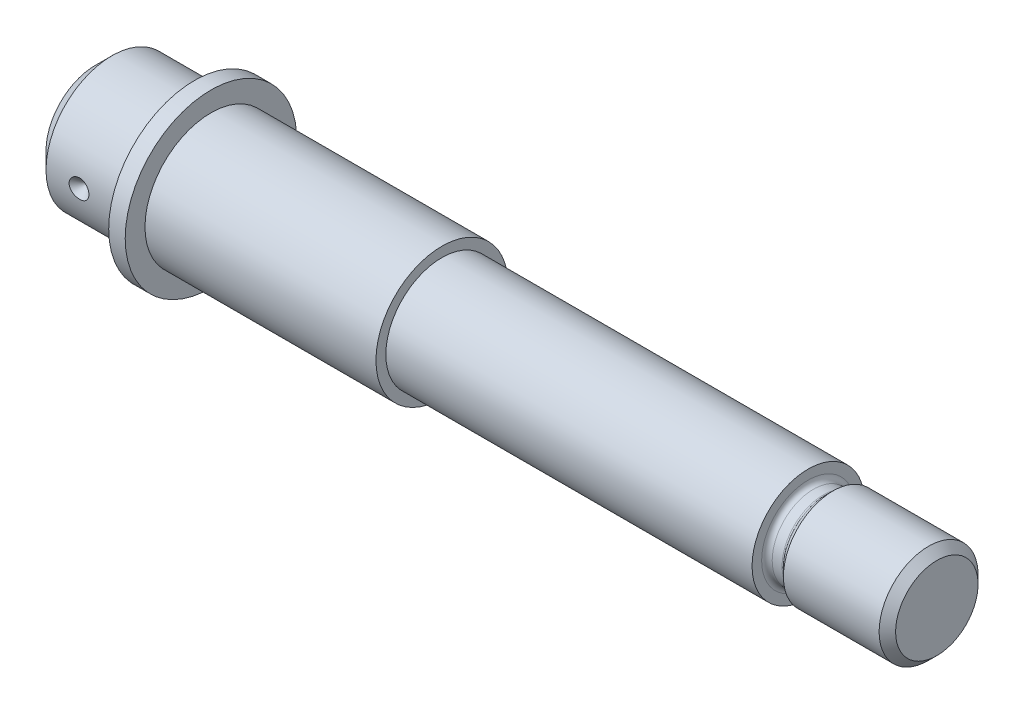
SolidWorks part; units mm, degrees
ref_plane "Front Plane" through (0, 0, 0) normal (0, 0, 1) x (1, 0, 0)
ref_plane "Top Plane" through (0, 0, 0) normal (0, 1, 0) x (1, 0, 0)
ref_plane "Right Plane" through (0, 0, 0) normal (1, 0, 0) x (0, 0, -1)
sketch "Sketch1" plane through (0, 0, 0) normal (0, 1, 0) x (1, 0, 0)
  line L0 (-87.7769, 0) -> (0, 0) construction
  line L1 (0, 0) -> (0, -15)
  line L2 (5, -20) -> (30, -20)
  line L3 (30, -20) -> (30, -26)
  line L4 (30, -26) -> (35, -26)
  line L5 (35, -26) -> (35, -20)
  line L6 (35, -20) -> (105, -20)
  line L7 (105, -20) -> (105, -17)
  line L8 (105, -17) -> (216, -17)
  line L9 (216, -17) -> (216, -15)
  line L10 (223.5, -15) -> (252.5, -15)
  line L11 (255, -12.5) -> (255, 0)
  line L12 (0, -15) -> (5, -20)
  line L13 (252.5, -15) -> (255, -12.5)
  line L14 (0, 0) -> (255, 0)
  line L15 (216, -15) -> (216, -14.1)
  line L16 (218.4967, -12.5) -> (217.6, -12.5) construction
  line L17 (30, -20) -> (35, -20) construction
  line L18 (216, -12.5) -> (216, -15) construction
  line L19 (217.6, -12.5) -> (220.5858, -12.5)
  line L20 (221.2929, -12.7929) -> (223.5, -15)
  line L21 (221, -12.5) -> (223.5, -12.5) construction
  line L22 (223.5, -12.5) -> (223.5, -15) construction
  arc A0 (216, -14.1) -> (217.6, -12.5) centre (217.6, -14.1) cw
  arc A2 (220.5858, -12.5) -> (221.2929, -12.7929) centre (220.5858, -13.5) cw
  point P4 (0, -20)
  point P15 (255, -15)
  point P24 (35, -23)
  point P26 (216, -12.5)
  point P34 (105, -18.5)
  dimension "D15" = 1.6
  dimension "D18" = 1
  dimension "D1" = 5
  dimension "D2" = 45
  dimension "D3" = 20
  dimension "D4" = 30
  dimension "D5" = 5
  dimension "D6" = 6
  dimension "D7" = 255
  dimension "D8" = 150
  dimension "D9" = 17
  dimension "D10" = 39
  dimension "D11" = 2.5
  dimension "D12" = 45
  dimension "D13" = 15
  dimension "D14" = 4.5
  dimension "D16" = 45
  dimension "D17" = 5
  dimension "D19" = 70
revolve "Revolve1" add sketch "Sketch1" angle 360 about L0
cosmetic thread "Cosmetic Thread1" parameters "D2"=26.2318
ref_plane "Plane1" through (0, 0, 20) normal (0, 0, 1) x (1, 0, 0)
sketch "Sketch4" plane through (0, 0, 20) normal (0, 0, 1) x (1, 0, 0)
  line L0 (5, 0) -> (30, 0) construction
  line L1 (5, 20) -> (5, -20) construction
  line L2 (30, 26) -> (30, -26) construction
  point P6 (15, 0)
  dimension "D1" = 10
ref_plane "Plane2" through (15, 0, 0) normal (-1, 0, 0) x (0, 0, 1)
sketch "Sketch5" plane through (15, 0, 0) normal (-1, 0, 0) x (0, 0, 1)
  line L0 (20, 0) -> (20, 3)
  line L1 (20, -13.75) -> (20, 13.75) construction
  line L2 (20, 3) -> (17, 0)
  line L3 (17, 0) -> (20, 0)
  dimension "D1" = 45
  dimension "D2" = 3
revolve "Cut-Revolve1" cut sketch "Sketch5" angle 360 about L3
ref_plane "Plane3" through (0, 0, -20) normal (0, 0, -1) x (-1, 0, 0)
sketch "Sketch6" plane through (0, 0, -20) normal (0, 0, -1) x (-1, 0, 0)
  line L0 (-105, 0) -> (-35, 0) construction
  line L1 (-105, 20) -> (-105, -20) construction
  line L2 (-35, 26) -> (-35, -26) construction
  line L3 (-73, 0) -> (-53, 0) construction
  line L4 (-73, 6) -> (-53, 6)
  line L5 (-73, -6) -> (-53, -6)
  arc A0 (-73, 6) -> (-73, -6) centre (-73, 0) ccw
  arc A1 (-53, -6) -> (-53, 6) centre (-53, 0) ccw
  point P8 (-63, 0)
  point P13 (-79, 0)
  point P14 (-47, 0)
  dimension "D1" = 6
  dimension "D2" = 32
  dimension "D3" = 12
extrude "Cut-Extrude1" cut sketch "Sketch6" against normal blind 4
